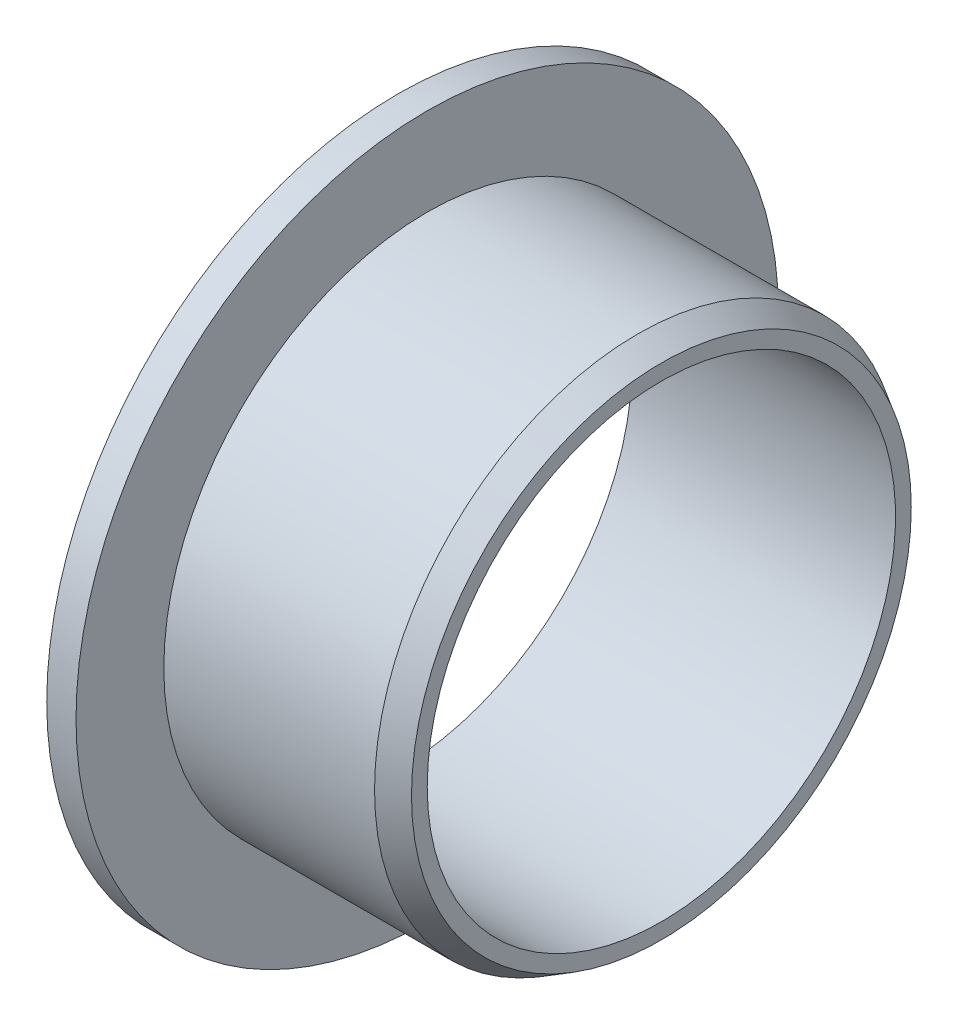
SolidWorks part; units mm, degrees
ref_plane "Płaszczyzna przednia" through (0, 0, 0) normal (0, 0, 1) x (1, 0, 0)
ref_plane "Płaszczyzna górna" through (0, 0, 0) normal (0, 1, 0) x (1, 0, 0)
ref_plane "Płaszczyzna prawa" through (0, 0, 0) normal (1, 0, 0) x (0, 0, -1)
sketch "Szkic1" plane through (0, 0, 0) normal (0, 0, 1) x (1, 0, 0)
  line L0 (0, 0) -> (0, 8) construction
  line L1 (0, 8) -> (9, 8)
  line L2 (0, 0) -> (24.2255, 0) construction
  line L3 (9, 8) -> (9, 9)
  line L4 (9, 9) -> (1, 9)
  line L5 (0, 8) -> (0, 12)
  line L6 (0, 12) -> (1, 12)
  line L7 (1, 12) -> (1, 9)
  point P10 (1, 10.5)
  dimension "D1" = 8
  dimension "D2" = 9
  dimension "D3" = 12
  dimension "D4" = 1
  dimension "D5" = 9
revolve "Obrót1" add sketch "Szkic1" angle 360 about L2
chamfer "Sfazowanie1" distance 0.8 angle 30 1 edges at (9, 0, 9)
